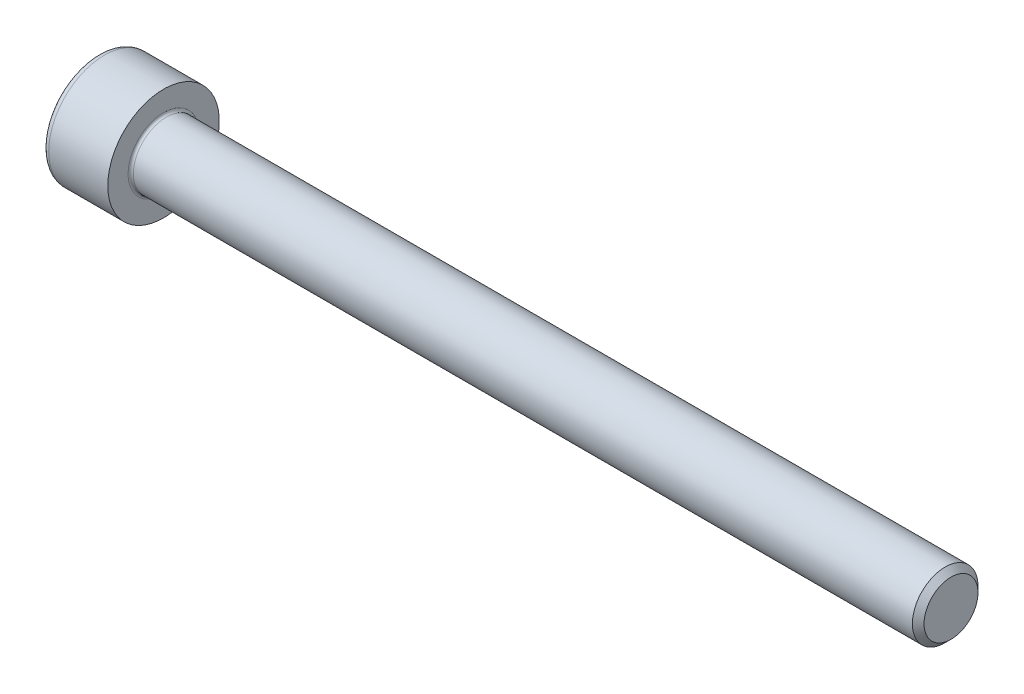
SolidWorks part; units mm, degrees
revolve "Base-Revolve" add sketch "BodySke"
sketch "BodySke" plane through (0, 0, 0) normal (0, 0, 1) x (1, 0, 0)
  line L0 (0, 0) -> (0, 4.25)
  line L1 (0, 4.25) -> (5, 4.25)
  line L2 (5, 4.25) -> (5, 2.5)
  line L3 (5, 2.5) -> (64.555, 2.5)
  line L4 (65, 2.055) -> (65, 0)
  line L5 (65, 0) -> (0, 0)
  line L6 (-31.75, 0) -> (127, 0) construction
  line L8 (65, 2.055) -> (64.555, 2.5)
  line L10 (65, -2.055) -> (64.555, -2.5) construction
  line L11 (5.8, 9.525) -> (5.8, 3.175) construction
  line L12 (43, 9.525) -> (43, 3.175) construction
  line L13 (35, 9.525) -> (35, 3.175) construction
  dimension "Head_ht" = 5
  dimension "Length" = 60
  dimension "Body_ch_ang" = 45
  dimension "Diameter" = 5
  dimension "Minor_dia" = 4.11
  dimension "Advance" = 0.8
  dimension "Thread_nom" = 22
  dimension "Thread_length" = 30
  dimension "Head_dia" = 8.5
cosmetic thread "ThreadCosmetic"
fillet "Fillet1" radius 0.2 1 edges at (5, 0, 2.5)
fillet "Fillet2" radius 0.5 1 edges at (0, 0, 4.25)
ref_plane "Plane1" through (0, 0, 0) normal (0, 0, 1) x (1, 0, 0)
ref_plane "Plane2" through (0, 0, 0) normal (0, 1, 0) x (1, 0, 0)
ref_plane "Plane3" through (0, 0, 0) normal (1, 0, 0) x (0, 0, -1)
sketch "Sketch2" plane through (0, 0, 0) normal (0, 0, 1) x (1, 0, 0)
  line L0 (0, 2.01) -> (2.5, 2.01)
  line L1 (2.5, 2.01) -> (3.6605, 0)
  line L2 (-31.75, 0) -> (127, 0) construction
  line L3 (3.6605, 0) -> (0, 0)
  line L4 (0, 0) -> (0, 2.01)
  line L6 (0, 0) -> (47.625, 0) construction
  dimension "D1" = 2.01
  dimension "D2" = 60
  dimension "Depth" = 2.5
revolve "Hex-PreBroach" cut sketch "Sketch2" angle 360 about L6
sketch "Sketch3" plane through (0, 0, 0) normal (-1, 0, 0) x (0, 0.5, 0.866)
  line L0 (1.1605, 2.01) -> (-1.1605, 2.01)
  line L1 (-1.1605, 2.01) -> (-2.3209, 0)
  line L2 (1.1605, 2.01) -> (2.3209, 0)
  line L3 (1.1605, -2.01) -> (2.3209, 0)
  line L4 (1.1605, -2.01) -> (-1.1605, -2.01)
  line L5 (-1.1605, -2.01) -> (-2.3209, 0)
  dimension "D1" = 2.01
  dimension "D2" = 2.01
  dimension "Hex_size" = 4.02
extrude "Hex" cut sketch "Sketch3" against normal blind 2.5
sketch "ThdSchSke" plane through (0, 0, 0) normal (0, 0, 1) x (1, 0, 0)
  line L0 (43, -2.055) -> (42.6884, -2.5)
  line L1 (43, -2.055) -> (43.3116, -2.5)
  line L2 (43.3116, -2.5) -> (43.3116, -3.125)
  line L3 (-3.175, 0) -> (5.1513, 0) construction
  line L4 (0, 3.75) -> (0, -3.75) construction
  line L5 (43.3116, -3.125) -> (42.6884, -3.125)
  line L6 (42.6884, -3.125) -> (42.6884, -2.5)
  dimension "Thread_minor" = 4.11
  dimension "Diameter" = 5
  dimension "Start" = 43
revolve "ThreadSchematic" [suppressed] cut sketch "ThdSchSke" angle 360 about L3
pattern_linear "ThdSchPat" [suppressed]
equation "\"D2@Sketch3\" = \"Hex_size@Sketch3\" / 2"
equation "\"D1@Sketch3\" = \"Hex_size@Sketch3\" / 2"
equation "\"D1@Sketch2\" = \"Hex_size@Sketch3\" / 2"
equation "\"Thread_minor@ThreadCosmetic\"  =  \"Minor_dia@BodySke\""
equation "\"Depth@Sketch2\" =  \"Key_eng@Hex\""
equation "\"Thread_length@ThreadCosmetic\" = ((sgn( (\"Length@BodySke\" - \"Advance@BodySke\" * 3.0) - \"Thread_nom@BodySke\" )-1)*( (\"Length@BodySke\" - \"Advance@BodySke\" * 3.0) - \"Thread_nom@BodySke\" ))/-2+ \"Thread_nom@BodySke\""
equation "\"Thread_minor@ThdSchSke\" = \"Minor_dia@BodySke\""
equation "\"Diameter@ThdSchSke\" = \"Diameter@BodySke\""
equation "\"Overcut@ThdSchSke\" = \"Diameter@BodySke\" * 1.25"
equation "\"Start@ThdSchSke\" = \"Head_ht@BodySke\" + \"Length@BodySke\" - \"Thread_length@ThreadCosmetic\"  '---Non-countersunk---"
equation "\"Num_threads@ThdSchPat\" = int( \"Thread_length@ThreadCosmetic\" / \"Advance@BodySke\" + 0.999 )  + 1"
equation "\"Advance@ThdSchPat\" = \"Thread_length@ThreadCosmetic\" /  (\"Num_threads@ThdSchPat\" - 1) 'relax it"
equation "\"Num_threads@ThdSchPat\" = \"Num_threads@ThdSchPat\" - sgn( \"Num_threads@ThdSchPat\" - 1) '---chamfered tips only---"
